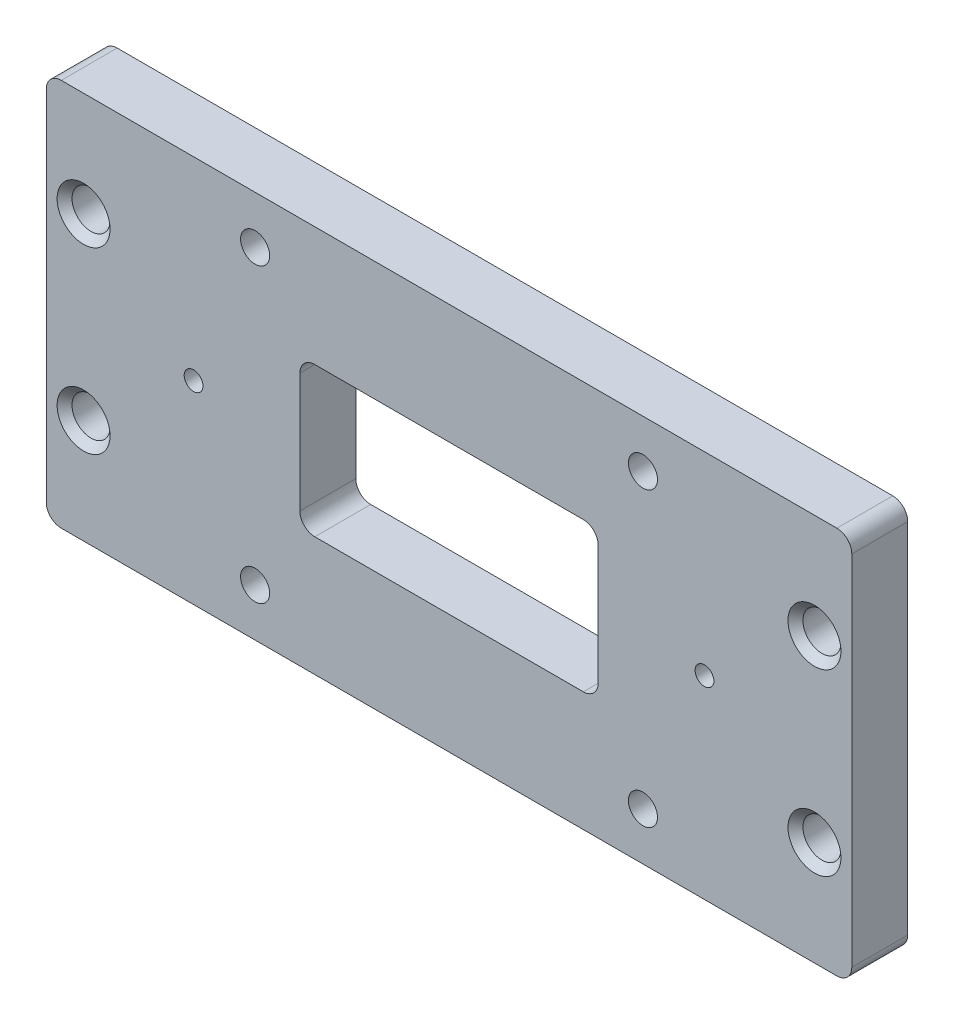
SolidWorks part; units mm, degrees
material "6061 Alloy"
ref_plane "Front Plane" through (0, 0, 0) normal (0, 0, 1) x (1, 0, 0)
ref_plane "Top Plane" through (0, 0, 0) normal (0, 1, 0) x (1, 0, 0)
ref_plane "Right Plane" through (0, 0, 0) normal (1, 0, 0) x (0, 0, -1)
sketch "Sketch1" plane through (0, 0, 0) normal (0, 0, 1) x (1, 0, 0)
  line L1 (-68.58, -33.02) -> (68.58, -33.02)
  line L2 (-68.58, -33.02) -> (-68.58, 33.02)
  line L3 (-68.58, 33.02) -> (68.58, 33.02)
  line L4 (68.58, -33.02) -> (68.58, 33.02)
  line L5 (-68.58, -33.02) -> (68.58, 33.02) construction
  line L6 (-68.58, 33.02) -> (68.58, -33.02) construction
  point P1 (0, 0)
  dimension "D1" = 137.16
  dimension "D2" = 66.04
extrude "Boss-Extrude1" add sketch "Sketch1" along normal blind 9.525
sketch "Sketch3" plane through (0, 0, 9.525) normal (0, 0, 1) x (1, 0, 0)
  line L0 (0, 37.178) -> (0, -44.4805) construction
  line L1 (-46.52, 0) -> (52.7512, 0) construction
  circle A0 centre (-33.02, 24.892) radius 2.4765
  circle A1 centre (33.02, 24.892) radius 2.4765
  circle A2 centre (33.02, -24.892) radius 2.4765
  circle A3 centre (-33.02, -24.892) radius 2.4765
  dimension "D1" = 4.953
  dimension "D2" = 33.02
  dimension "D3" = 24.892
extrude "Cut-Extrude1" cut sketch "Sketch3" against normal through all
sketch "Sketch4" plane through (0, 0, 9.525) normal (0, 0, 1) x (1, 0, 0)
  line L0 (-64.9061, 0) -> (67.7138, 0) construction
  line L1 (0, 36.2516) -> (0, -42.6927) construction
  circle A0 centre (-62.23, 15.24) radius 3.2385
  circle A1 centre (62.23, 15.24) radius 3.2385
  circle A2 centre (62.23, -15.24) radius 3.2385
  circle A3 centre (-62.23, -15.24) radius 3.2385
  dimension "D1" = 6.477
  dimension "D2" = 62.23
  dimension "D3" = 15.24
extrude "Cut-Extrude2" cut sketch "Sketch4" against normal up to next
sketch "Sketch5" plane through (0, 0, 9.525) normal (0, 0, 1) x (1, 0, 0)
  line L0 (-60.2818, 0) -> (55.3271, 0) construction
  line L1 (0, 36.582) -> (0, -43.5185) construction
  circle A0 centre (-43.5, 0) radius 1.6
  circle A1 centre (43.5, 0) radius 1.6
  dimension "D1" = 3.2
  dimension "D2" = 43.5
extrude "Cut-Extrude3" cut sketch "Sketch5" against normal up to next
sketch "Sketch6" plane through (0, 0, 9.525) normal (0, 0, 1) x (1, 0, 0)
  line L1 (-25.4, -12.7) -> (25.4, -12.7)
  line L2 (-25.4, -12.7) -> (-25.4, 12.7)
  line L3 (-25.4, 12.7) -> (25.4, 12.7)
  line L4 (25.4, -12.7) -> (25.4, 12.7)
  line L5 (-25.4, -12.7) -> (25.4, 12.7) construction
  line L6 (-25.4, 12.7) -> (25.4, -12.7) construction
  point P0 (0, 0)
  dimension "D1" = 50.8
  dimension "D2" = 25.4
extrude "Cut-Extrude4" cut sketch "Sketch6" against normal up to next
fillet "Fillet1" radius 2.54 4 edges at (-68.58, -33.02, 4.7625) (-68.58, 33.02, 4.7625) (68.58, -33.02, 4.7625) (68.58, 33.02, 4.7625)
fillet "Fillet2" radius 2.54 4 edges at (-25.4, -12.7, 4.7625) (25.4, 12.7, 4.7625) (25.4, -12.7, 4.7625) (-25.4, 12.7, 4.7625)
chamfer "Chamfer1" distance 1.27 angle 45 8 edges at (-65.4685, -15.24, 0) (-65.4685, 15.24, 0) (58.9915, -15.24, 0) (58.9915, 15.24, 0) (65.4685, -15.24, 9.525) (58.9915, 15.24, 9.525) (-65.4685, -15.24, 9.525) (-58.9915, 15.24, 9.525)
